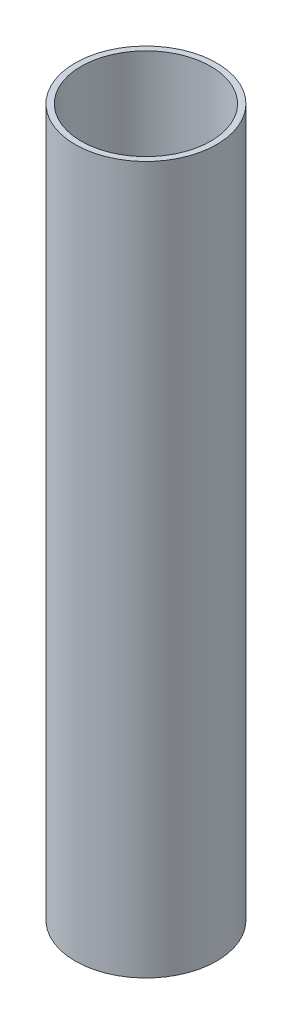
SolidWorks part; units mm, degrees
material "Wrought Stainless Steel"
ref_plane "Front Plane" through (0, 0, 0) normal (0, 0, 1) x (1, 0, 0)
ref_plane "Top Plane" through (0, 0, 0) normal (0, 1, 0) x (1, 0, 0)
ref_plane "Right Plane" through (0, 0, 0) normal (1, 0, 0) x (0, 0, -1)
sketch "Sketch1" plane through (0, 0, 0) normal (0, 1, 0) x (1, 0, 0)
  circle A0 centre (0, 0) radius 76.2
  circle A1 centre (0, 0) radius 69.85
  dimension "D1" = 152.4
  dimension "D2" = 6.35
extrude "Boss-Extrude1" add sketch "Sketch1" along normal blind 762
